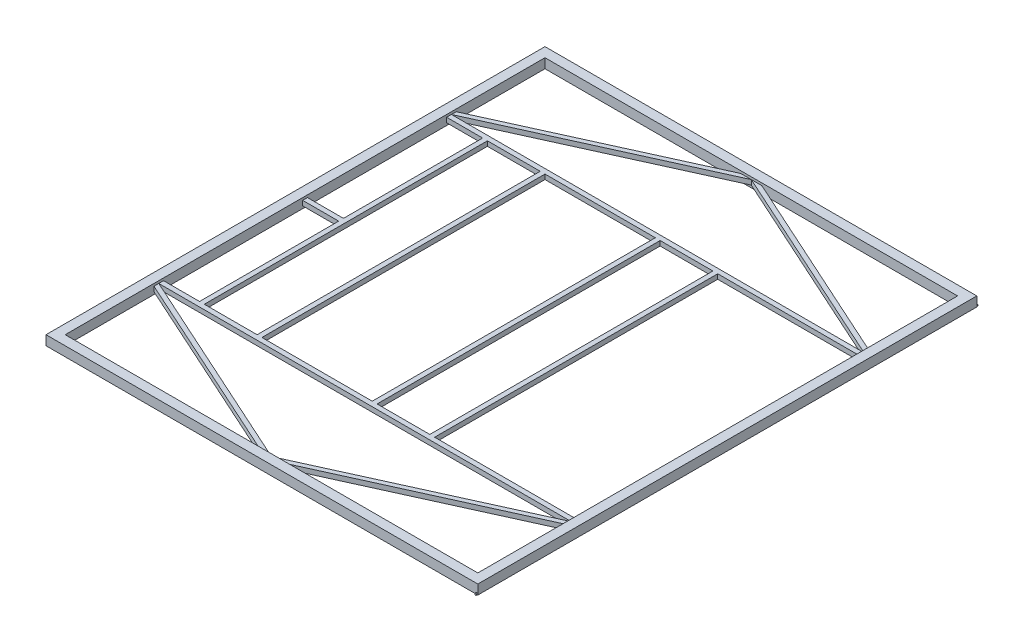
SolidWorks part; units mm, degrees
material "2219-T87"
ref_plane "Front Plane" through (0, 0, 0) normal (0, 0, 1) x (1, 0, 0)
ref_plane "Top Plane" through (0, 0, 0) normal (0, 1, 0) x (1, 0, 0)
ref_plane "Right Plane" through (0, 0, 0) normal (1, 0, 0) x (0, 0, -1)
sketch "Sketch1" plane through (0, 0, 0) normal (0, 0, 1) x (1, 0, 0)
  line L1 (1092.2, 25.4) -> (1143, 25.4)
  line L2 (1092.2, 25.4) -> (1092.2, -25.4)
  line L3 (1092.2, -25.4) -> (1143, -25.4)
  line L4 (1143, 25.4) -> (1143, -25.4)
  line L5 (1092.2, 25.4) -> (1143, -25.4) construction
  line L6 (1092.2, -25.4) -> (1143, 25.4) construction
  line L7 (1093.7875, 23.8125) -> (1141.4125, 23.8125)
  line L8 (1093.7875, 23.8125) -> (1093.7875, -23.8125)
  line L9 (1093.7875, -23.8125) -> (1141.4125, -23.8125)
  line L10 (1141.4125, 23.8125) -> (1141.4125, -23.8125)
  line L11 (1093.7875, 23.8125) -> (1141.4125, -23.8125) construction
  line L12 (1093.7875, -23.8125) -> (1141.4125, 23.8125) construction
  point P0 (1117.6, 0)
  point P5 (1117.6, 0)
  dimension "D1" = 50.8
  dimension "D2" = 50.8
  dimension "D3" = 47.625
  dimension "D4" = 47.625
  dimension "D5" = 1117.6
sketch "Sketch2" plane through (0, 0, 0) normal (0, 1, 0) x (1, 0, 0)
  line L1 (-1117.6, 1295.4) -> (1117.6, 1295.4)
  line L2 (-1117.6, 1295.4) -> (-1117.6, -1295.4)
  line L3 (-1117.6, -1295.4) -> (1117.6, -1295.4)
  line L4 (1117.6, 1295.4) -> (1117.6, -1295.4)
  line L5 (-1117.6, 1295.4) -> (1117.6, -1295.4) construction
  line L6 (-1117.6, -1295.4) -> (1117.6, 1295.4) construction
  point P0 (0, 0)
  dimension "D1" = 2235.2
  dimension "D2" = 2590.8
sweep "Sweep1" add profiles "Sketch1" path "Sketch2"
sketch "Sketch3" plane through (0, 0, -1320.8) normal (0, 0, -1) x (-1, 0, 0)
  line L0 (-1143, 25.4) -> (-1143, -25.4) construction
  line L1 (1143, -25.4) -> (-1143, -25.4) construction
  circle A0 centre (-1138.2375, -20.6375) radius 4.7625
  dimension "D1" = 9.525
  dimension "D2" = 4.7625
  dimension "D3" = 4.7625
extrude "Boss-Extrude1" add sketch "Sketch3" along normal blind 6.35 contours A0
sketch "Sketch4" plane through (0, 0, 1320.8) normal (0, 0, 1) x (1, 0, 0)
  line L1 (1143, -25.4) -> (-1143, -25.4) construction
  line L2 (1143, 25.4) -> (1143, -25.4) construction
  circle A0 centre (1138.2375, -20.6375) radius 4.7625
  dimension "D1" = 9.525
  dimension "D2" = 4.7625
  dimension "D3" = 4.7625
extrude "Boss-Extrude2" add sketch "Sketch4" along normal blind 6.35 contours A0
sketch "Sketch5" plane through (-1092.2, 0, 0) normal (1, 0, 0) x (0, 0, -1)
  line L0 (-1270, 25.4) -> (1270, 25.4) construction
  line L1 (-774.7, 12.7) -> (-749.3, 12.7)
  line L2 (-774.7, 12.7) -> (-774.7, -12.7)
  line L3 (-774.7, -12.7) -> (-749.3, -12.7)
  line L4 (-749.3, 12.7) -> (-749.3, -12.7)
  line L5 (-774.7, 12.7) -> (-749.3, -12.7) construction
  line L6 (-774.7, -12.7) -> (-749.3, 12.7) construction
  line L7 (-1270, -25.4) -> (-1270, 25.4) construction
  line L8 (-752.475, 9.525) -> (-752.475, -9.525)
  line L9 (-771.525, -9.525) -> (-752.475, -9.525)
  line L10 (-771.525, 9.525) -> (-771.525, -9.525)
  line L11 (-771.525, 9.525) -> (-752.475, 9.525)
  line L12 (749.3, 12.7) -> (749.3, -12.7)
  line L13 (749.3, 12.7) -> (774.7, 12.7)
  line L14 (774.7, 12.7) -> (774.7, -12.7)
  line L15 (749.3, -12.7) -> (774.7, -12.7)
  line L16 (771.525, 9.525) -> (771.525, -9.525)
  line L17 (752.475, -9.525) -> (771.525, -9.525)
  line L18 (752.475, 9.525) -> (752.475, -9.525)
  line L19 (752.475, 9.525) -> (771.525, 9.525)
  line L20 (1270, -25.4) -> (1270, 25.4) construction
  point P0 (-762, 0)
  point P9 (-1270, 0)
  point P14 (762, 12.7)
  dimension "D1" = 25.4
  dimension "D2" = 25.4
  dimension "D3" = 25.4
  dimension "D4" = 508
  dimension "D7" = 508
  dimension "D5" = 3.175
  dimension "D6" = 2
extrude "Boss-Extrude3" add sketch "Sketch5" along normal up to surface (2184.4 mm away) up to face at (1092.2, 0, 0)
sketch "Sketch6" plane through (0, 0, 749.3) normal (0, 0, -1) x (-1, 0, 0)
  line L0 (-1092.2, -12.7) -> (1092.2, -12.7) construction
  line L1 (-317.5, 12.7) -> (-342.9, 12.7)
  line L2 (-317.5, 12.7) -> (-317.5, -12.7)
  line L3 (-317.5, -12.7) -> (-342.9, -12.7)
  line L4 (-342.9, 12.7) -> (-342.9, -12.7)
  line L5 (-317.5, 12.7) -> (-342.9, -12.7) construction
  line L6 (-317.5, -12.7) -> (-342.9, 12.7) construction
  line L7 (-1092.2, 12.7) -> (1092.2, 12.7) construction
  line L8 (-1092.2, 12.7) -> (-1092.2, -12.7) construction
  line L9 (-12.7, 12.7) -> (-38.1, 12.7)
  line L10 (-12.7, 12.7) -> (-12.7, -12.7)
  line L11 (-12.7, -12.7) -> (-38.1, -12.7)
  line L12 (-38.1, 12.7) -> (-38.1, -12.7)
  line L13 (-12.7, 12.7) -> (-38.1, -12.7) construction
  line L14 (-12.7, -12.7) -> (-38.1, 12.7) construction
  line L15 (-320.675, 9.525) -> (-320.675, -9.525)
  line L16 (-320.675, -9.525) -> (-339.725, -9.525)
  line L17 (-339.725, 9.525) -> (-339.725, -9.525)
  line L18 (-320.675, 9.525) -> (-339.725, 9.525)
  line L19 (-15.875, 9.525) -> (-34.925, 9.525)
  line L20 (-34.925, 9.525) -> (-34.925, -9.525)
  line L21 (-15.875, -9.525) -> (-34.925, -9.525)
  line L22 (-15.875, 9.525) -> (-15.875, -9.525)
  line L23 (596.9, 12.7) -> (596.9, -12.7)
  line L24 (596.9, 12.7) -> (571.5, 12.7)
  line L25 (571.5, 12.7) -> (571.5, -12.7)
  line L26 (596.9, -12.7) -> (571.5, -12.7)
  line L27 (593.725, 9.525) -> (593.725, -9.525)
  line L28 (593.725, -9.525) -> (574.675, -9.525)
  line L29 (574.675, 9.525) -> (574.675, -9.525)
  line L30 (593.725, 9.525) -> (574.675, 9.525)
  line L31 (901.7, 12.7) -> (876.3, 12.7)
  line L32 (876.3, 12.7) -> (876.3, -12.7)
  line L33 (901.7, -12.7) -> (876.3, -12.7)
  line L34 (901.7, 12.7) -> (901.7, -12.7)
  line L35 (898.525, 9.525) -> (879.475, 9.525)
  line L36 (879.475, 9.525) -> (879.475, -9.525)
  line L37 (898.525, -9.525) -> (879.475, -9.525)
  line L38 (898.525, 9.525) -> (898.525, -9.525)
  point P0 (-330.2, 0)
  point P11 (-25.4, 0)
  point P24 (584.2, -12.7)
  dimension "D1" = 25.4
  dimension "D2" = 762
  dimension "D3" = 25.4
  dimension "D4" = 304.8
  dimension "D8" = 609.6
  dimension "D5" = 3.175
  dimension "D6" = 3.175
  dimension "D7" = 2
extrude "Boss-Extrude4" add sketch "Sketch6" along normal up to surface (1498.6 mm away) up to face at (0, 0, -749.3)
sketch "Sketch7" plane through (1092.2, 0, 0) normal (-1, 0, 0) x (0, 0, 1)
  line L1 (-774.7, -12.7) -> (-800.1, -12.7)
  line L2 (-774.7, -12.7) -> (-774.7, 12.7)
  line L3 (-774.7, 12.7) -> (-800.1, 12.7)
  line L4 (-800.1, -12.7) -> (-800.1, 12.7)
  line L5 (-774.7, -12.7) -> (-800.1, 12.7) construction
  line L6 (-774.7, 12.7) -> (-800.1, -12.7) construction
  line L11 (-777.875, -9.525) -> (-777.875, 9.525)
  line L12 (-777.875, 9.525) -> (-796.925, 9.525)
  line L13 (-796.925, -9.525) -> (-796.925, 9.525)
  line L14 (-777.875, -9.525) -> (-796.925, -9.525)
  line L15 (-774.7, 12.7) -> (-774.7, -12.7) construction
  point P0 (-787.4, 0)
  point P13 (-774.7, 0)
  point P14 (-774.7, 0)
  dimension "D1" = 25.4
  dimension "D2" = 25.4
  dimension "D3" = 3.175
sketch "Sketch8" plane through (0, 25.4, 0) normal (0, 1, 0) x (1, 0, 0)
  line L0 (-1092.2, 774.7) -> (0, 1270)
  line L2 (0, 1270) -> (1092.2, 774.7)
  line L3 (1092.2, 1270) -> (1092.2, -1270) construction
  line L4 (-1092.2, 1270) -> (1092.2, 1270) construction
sketch "Sketch9" plane through (1092.2, 0, 0) normal (-1, 0, 0) x (0, 0, 1)
  line L0 (774.7, -12.7) -> (774.7, 12.7) construction
  line L1 (800.1, -12.7) -> (774.7, -12.7)
  line L2 (800.1, -12.7) -> (800.1, 12.7)
  line L3 (800.1, 12.7) -> (774.7, 12.7)
  line L4 (774.7, -12.7) -> (774.7, 12.7)
  line L5 (800.1, -12.7) -> (774.7, 12.7) construction
  line L6 (800.1, 12.7) -> (774.7, -12.7) construction
  line L7 (796.925, -9.525) -> (796.925, 9.525)
  line L8 (796.925, 9.525) -> (777.875, 9.525)
  line L9 (777.875, -9.525) -> (777.875, 9.525)
  line L10 (796.925, -9.525) -> (777.875, -9.525)
  point P0 (787.4, 0)
  point P5 (774.7, 0)
  point P8 (774.7, 0)
  dimension "D1" = 25.4
  dimension "D2" = 25.4
  dimension "D3" = 3.175
sketch "Sketch10" plane through (0, 25.4, 0) normal (0, 1, 0) x (1, 0, 0)
  line L0 (1092.2, -774.7) -> (0, -1270)
  line L2 (1092.2, -1270) -> (-1092.2, -1270) construction
  line L3 (0, -1270) -> (-1092.2, -774.7)
  line L4 (1092.2, -800.1) -> (1092.2, -774.7) construction
  line L5 (1092.2, -774.7) -> (-1092.2, -774.7) construction
sweep "Sweep2" add profiles "Sketch9" path "Sketch10"
sweep "Sweep4" add profiles "Sketch7" path "Sketch8"
sketch "Sketch11" plane through (-901.7, 0, 0) normal (-1, 0, 0) x (0, 0, 1)
  line L0 (-749.3, -12.7) -> (749.3, -12.7) construction
  line L1 (12.7, -12.7) -> (-12.7, -12.7)
  line L2 (12.7, -12.7) -> (12.7, 12.7)
  line L3 (12.7, 12.7) -> (-12.7, 12.7)
  line L4 (-12.7, -12.7) -> (-12.7, 12.7)
  line L5 (12.7, -12.7) -> (-12.7, 12.7) construction
  line L6 (12.7, 12.7) -> (-12.7, -12.7) construction
  line L7 (-749.3, 12.7) -> (749.3, 12.7) construction
  line L8 (9.525, -9.525) -> (9.525, 9.525)
  line L9 (9.525, 9.525) -> (-9.525, 9.525)
  line L10 (-9.525, -9.525) -> (-9.525, 9.525)
  line L11 (9.525, -9.525) -> (-9.525, -9.525)
  point P0 (0, 0)
  point P12 (0, -12.7)
  point P13 (0, -12.7)
  dimension "D1" = 25.4
  dimension "D2" = 3.175
extrude "Boss-Extrude5" add sketch "Sketch11" along normal up to surface (190.5 mm away) up to face at (-1092.2, 0, 0)
